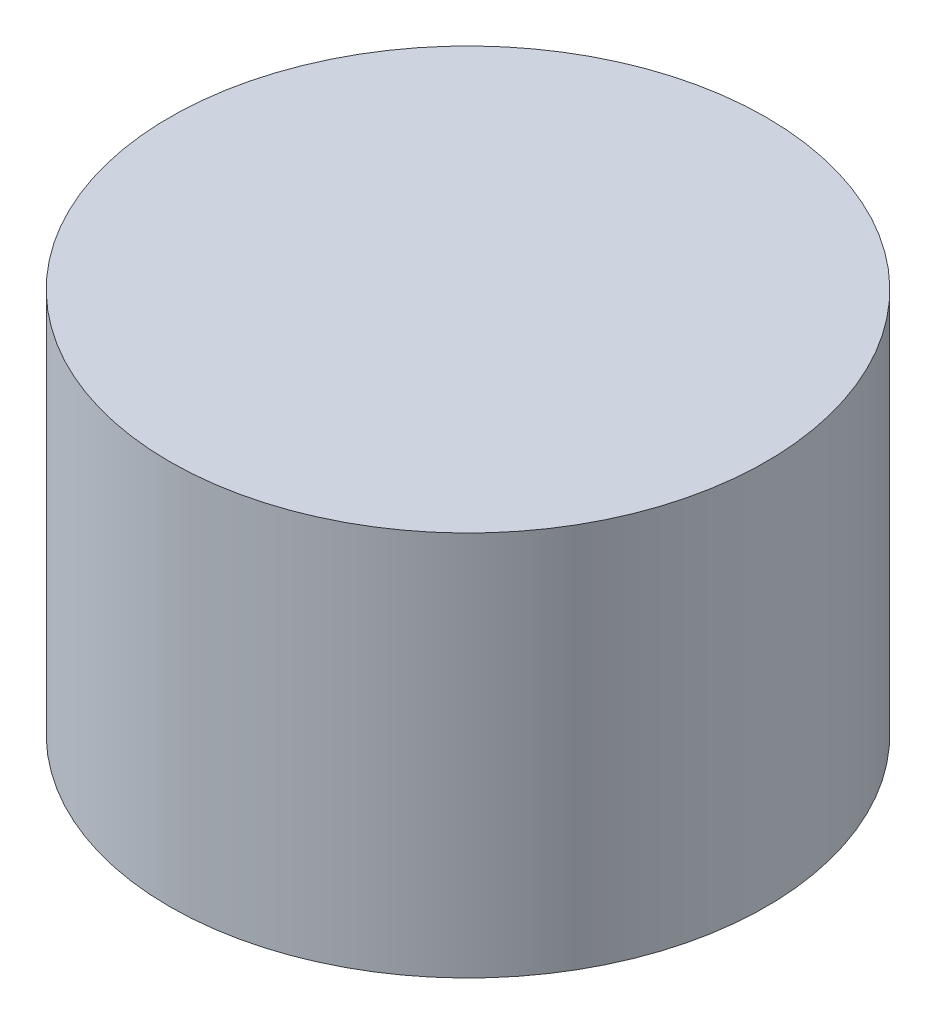
SolidWorks part; units mm, degrees
ref_plane "Front" through (0, 0, 0) normal (0, 0, 1) x (1, 0, 0)
ref_plane "Top" through (0, 0, 0) normal (0, 1, 0) x (1, 0, 0)
ref_plane "Right" through (0, 0, 0) normal (1, 0, 0) x (0, 0, -1)
sketch "Sketch1" plane through (0, 0, 0) normal (0, 1, 0) x (1, 0, 0)
  circle A1 centre (0, 0) radius 4.9145
extrude "Boss-Extrude1" add sketch "Sketch1" along normal blind 6.35
